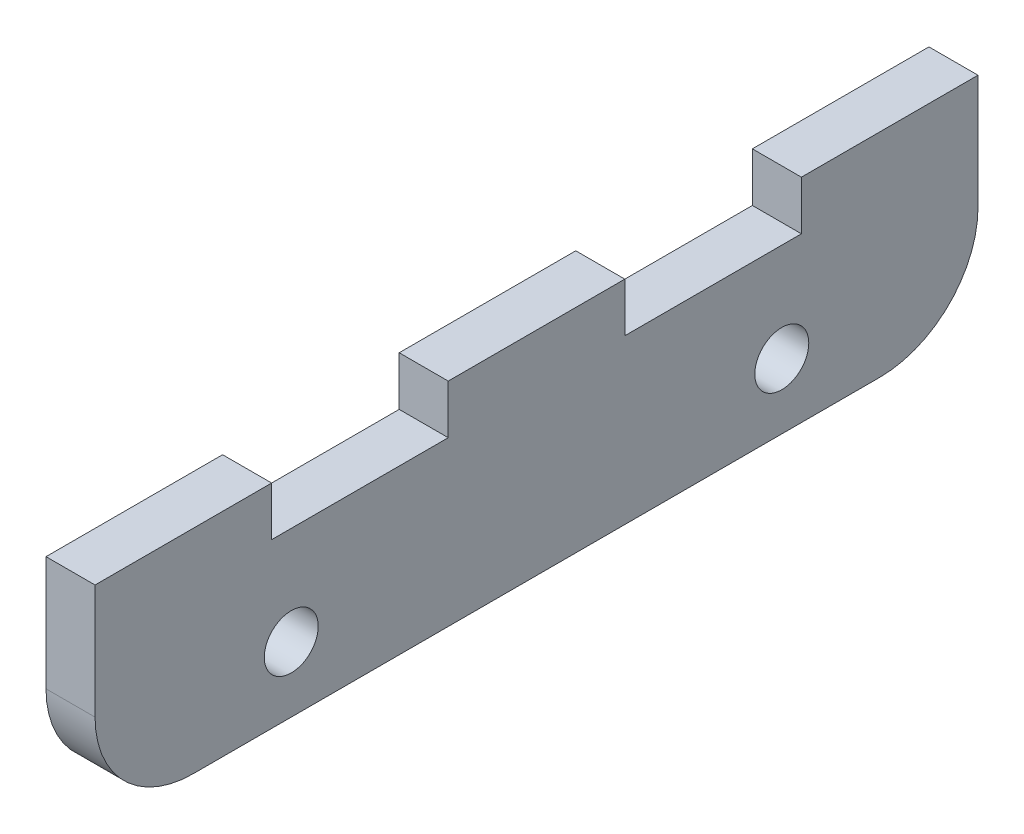
SolidWorks part; units mm, degrees
ref_plane "Ön Düzlem" through (0, 0, 0) normal (0, 0, 1) x (1, 0, 0)
ref_plane "Üst Düzlem" through (0, 0, 0) normal (0, 1, 0) x (1, 0, 0)
ref_plane "Sağ Düzlem" through (0, 0, 0) normal (1, 0, 0) x (0, 0, -1)
sketch "Sketch1" plane through (0, 0, 0) normal (1, 0, 0) x (0, 0, -1)
  line L1 (21, -6.5) -> (-21, -6.5)
  line L2 (27, -0.5) -> (27, 6.5)
  line L3 (27, 6.5) -> (16.2, 6.5)
  line L4 (-27, -0.5) -> (-27, 6.5)
  line L5 (27, -6.5) -> (-27, 6.5) construction
  line L6 (27, 6.5) -> (-27, -6.5) construction
  line L7 (-27, 6.5) -> (-16.2, 6.5)
  line L8 (5.4, 6.5) -> (-5.4, 6.5)
  line L11 (16.2, 6.5) -> (16.2, 3.5)
  line L12 (16.2, 3.5) -> (5.4, 3.5)
  line L14 (-5.4, 3.5) -> (-16.2, 3.5)
  line L17 (5.4, 3.5) -> (5.4, 6.5)
  line L18 (-5.4, 3.5) -> (-5.4, 6.5)
  line L19 (-16.2, 3.5) -> (-16.2, 6.5)
  circle A0 centre (-15, -2.509) radius 1.65
  circle A1 centre (15, -2.509) radius 1.65
  arc A2 (-21, -6.5) -> (-27, -0.5) centre (-21, -0.5) cw
  arc A3 (27, -0.5) -> (21, -6.5) centre (21, -0.5) cw
  point P0 (0, 0)
  dimension "D3" = 6
  dimension "D4" = 6
  dimension "D1" = 54
  dimension "D2" = 13
extrude "Boss-Extrude1" add sketch "Sketch1" along normal blind 3
